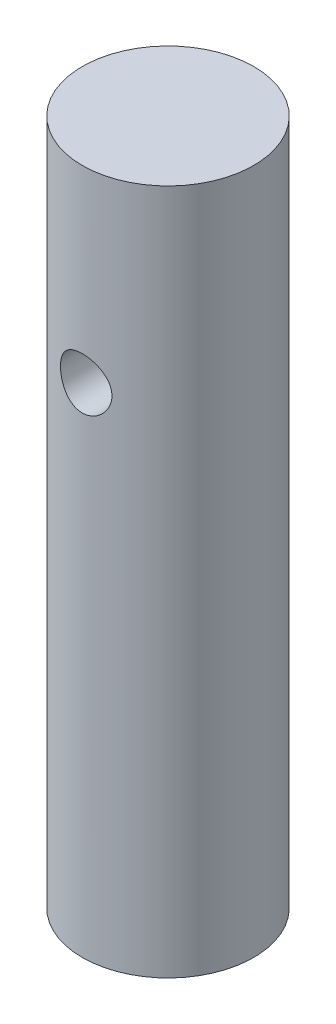
SolidWorks part; units mm, degrees
ref_plane "Alzado" through (0, 0, 0) normal (0, 0, 1) x (1, 0, 0)
ref_plane "Planta" through (0, 0, 0) normal (0, 1, 0) x (1, 0, 0)
ref_plane "Vista lateral" through (0, 0, 0) normal (1, 0, 0) x (0, 0, -1)
sketch "Croquis1" plane through (0, 0, 0) normal (0, 1, 0) x (1, 0, 0)
  circle A0 centre (0, 0) radius 2.5
  dimension "D1" = 5
extrude "Saliente-Extruir1" add sketch "Croquis1" along normal blind 20
sketch "Croquis2" plane through (0, 0, 0) normal (0, 0, 1) x (1, 0, 0)
  line L0 (2.5, 20) -> (-2.5, 20) construction
  circle A0 centre (0, 14.5) radius 0.75
  dimension "D2" = 1.5
  dimension "D1" = 5.5
extrude "Cortar-Extruir1" cut sketch "Croquis2" against normal up to surface and the other way up to surface up to face at (0, 20, 2.5) other way up to face at (0, 20, 2.5)
